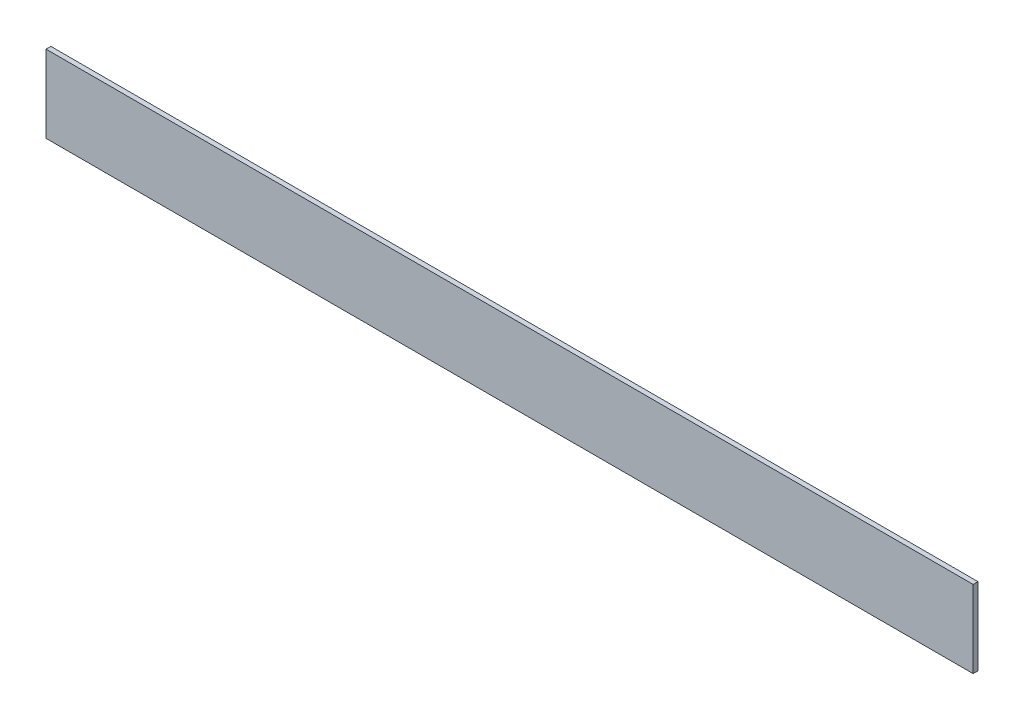
SolidWorks part; units mm, degrees
material "Acrylic (Medium-high impact)"
ref_plane "Front Plane" through (0, 0, 0) normal (0, 0, 1) x (1, 0, 0)
ref_plane "Top Plane" through (0, 0, 0) normal (0, 1, 0) x (1, 0, 0)
ref_plane "Right Plane" through (0, 0, 0) normal (1, 0, 0) x (0, 0, -1)
sketch "Sketch1" plane through (0, 0, 0) normal (0, 0, 1) x (1, 0, 0)
  line L1 (-304.8, 25.4) -> (304.8, 25.4)
  line L2 (-304.8, 25.4) -> (-304.8, -25.4)
  line L3 (-304.8, -25.4) -> (304.8, -25.4)
  line L4 (304.8, 25.4) -> (304.8, -25.4)
  line L5 (-304.8, 25.4) -> (304.8, -25.4) construction
  line L6 (-304.8, -25.4) -> (304.8, 25.4) construction
  point P0 (0, 0)
  dimension "D1" = 609.6
  dimension "D2" = 50.8
extrude "Boss-Extrude1" add sketch "Sketch1" along normal blind 3.175
